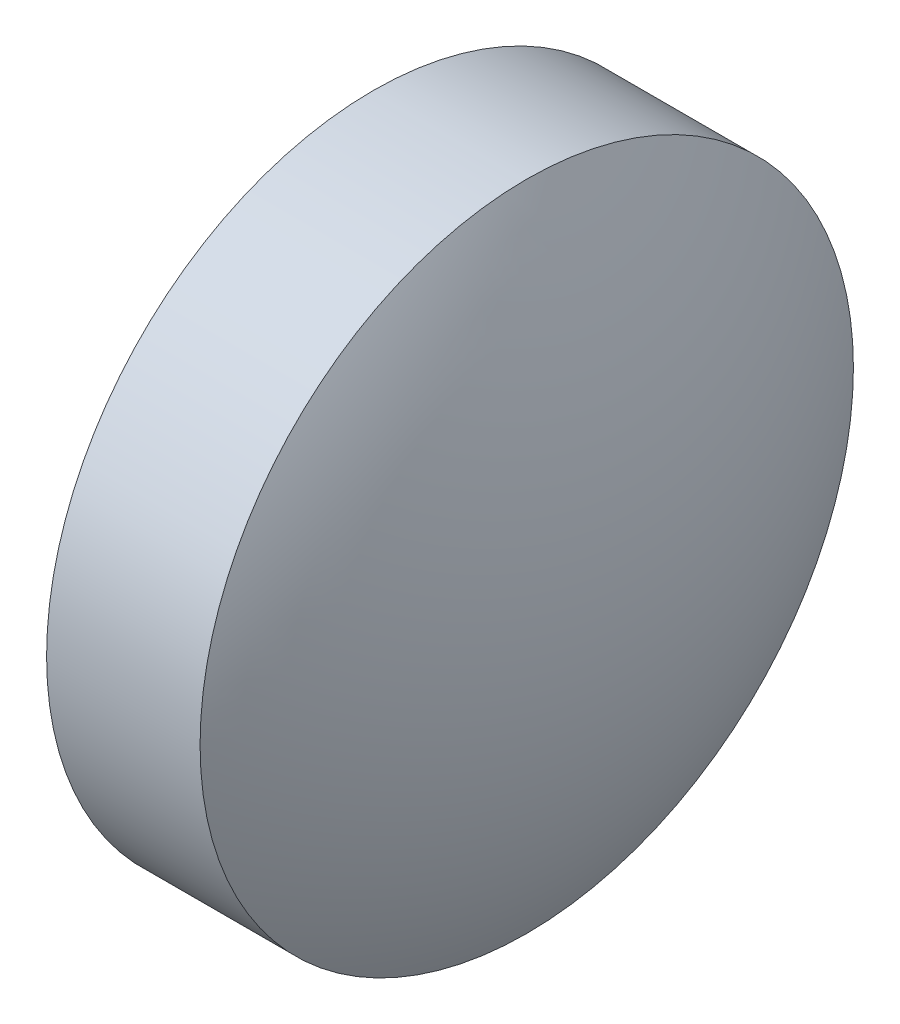
SolidWorks part; units mm, degrees
ref_plane "前视基准面" through (0, 0, 0) normal (0, 0, 1) x (1, 0, 0)
ref_plane "上视基准面" through (0, 0, 0) normal (0, 1, 0) x (1, 0, 0)
ref_plane "右视基准面" through (0, 0, 0) normal (1, 0, 0) x (0, 0, -1)
sketch "草图1" plane through (0, 0, 0) normal (0, 0, 1) x (1, 0, 0)
  line L0 (492.7766, 162.5923) -> (546.5596, 162.5923) construction
  line L1 (510.9932, 162.5923) -> (510.9932, 165.7423)
  line L2 (510.9932, 162.5923) -> (513.2932, 162.5923)
  line L3 (510.9932, 165.7423) -> (512.4732, 165.7423)
  arc A0 (513.2932, 162.5923) -> (512.4732, 165.7423) centre (506.8329, 162.5923) ccw
revolve "旋转1" add sketch "草图1" angle 360 about L0
